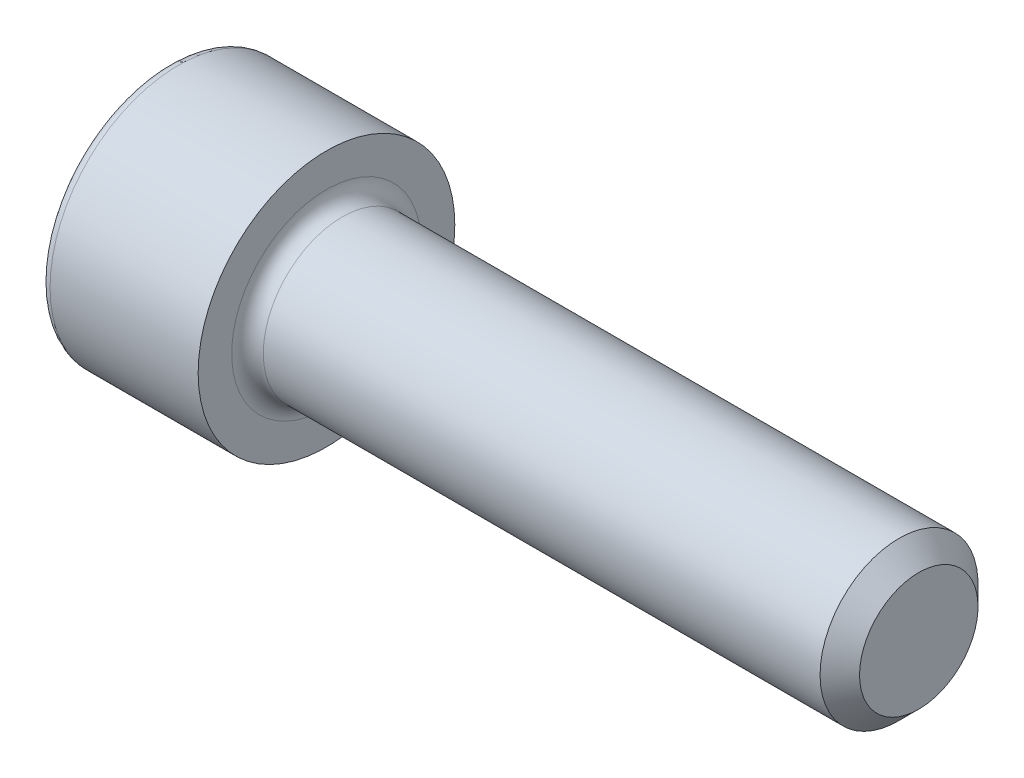
SolidWorks part; units mm, degrees
ref_plane "Plane1" through (0, 0, 0) normal (0, 0, 1) x (1, 0, 0)
ref_plane "Plane2" through (0, 0, 0) normal (0, 1, 0) x (1, 0, 0)
ref_plane "Plane3" through (0, 0, 0) normal (1, 0, 0) x (0, 0, -1)
sketch "BodySke" plane through (0, 0, 0) normal (0, 0, 1) x (1, 0, 0)
  line L0 (0, 0) -> (0, 6.5)
  line L1 (0, 6.5) -> (8, 6.5)
  line L2 (8, 6.5) -> (8, 4)
  line L3 (8, 4) -> (37, 4)
  line L4 (38, 3) -> (38, 0)
  line L5 (38, 0) -> (0, 0)
  line L6 (-31.75, 0) -> (127, 0) construction
  line L8 (38, 3) -> (37, 4)
  line L10 (38, -3) -> (37, -4) construction
  line L11 (5, 9.525) -> (5, 3.175) construction
  line L12 (8, 9.525) -> (8, 3.175) construction
  line L13 (-7, 9.525) -> (-7, 3.175) construction
  dimension "Head_ht" = 8
  dimension "Length" = 30
  dimension "Body_ch_ang" = 45
  dimension "Diameter" = 8
  dimension "Minor_dia" = 6
  dimension "Advance" = 3
  dimension "Thread_nom" = 30
  dimension "Thread_length" = 45
  dimension "Head_dia" = 13
revolve "Base-Revolve" add sketch "BodySke" angle 360 about L6
cosmetic thread "ThreadCosmetic" parameters "Thread_length"=21, "Thread_minor"=6
fillet "Fillet1" radius 0.8 1 edges at (8, 0, 4)
fillet "Fillet2" radius 0.5 1 edges at (0, 0, 6.5)
sketch "Sketch2" plane through (0, 0, 0) normal (0, 0, 1) x (1, 0, 0)
  line L0 (0, 2.8475) -> (12.573, 2.8475)
  line L1 (12.573, 2.8475) -> (14.217, 0)
  line L2 (-31.75, 0) -> (127, 0) construction
  line L3 (14.217, 0) -> (0, 0)
  line L4 (0, 0) -> (0, 2.8475)
  line L6 (0, 0) -> (47.625, 0) construction
  dimension "D1" = 2.8475
  dimension "D2" = 60
  dimension "Depth" = 12.573
revolve "Hex-PreBroach" cut sketch "Sketch2" angle 360 about L6
sketch "Sketch3" plane through (0, 0, 0) normal (-1, 0, 0) x (0, 0.5, 0.866)
  line L0 (1.644, 2.8475) -> (-1.644, 2.8475)
  line L1 (-1.644, 2.8475) -> (-3.288, 0)
  line L2 (1.644, 2.8475) -> (3.288, 0)
  line L3 (1.644, -2.8475) -> (3.288, 0)
  line L4 (1.644, -2.8475) -> (-1.644, -2.8475)
  line L5 (-1.644, -2.8475) -> (-3.288, 0)
  dimension "D1" = 2.8475
  dimension "D2" = 2.8475
  dimension "Hex_size" = 5.695
extrude "Hex" cut sketch "Sketch3" against normal blind 12.573
sketch "ThdSchSke" plane through (0, 0, 0) normal (0, 0, 1) x (1, 0, 0)
  line L0 (17, -3) -> (16.2998, -4)
  line L1 (17, -3) -> (17.7002, -4)
  line L2 (17.7002, -4) -> (17.7002, -5)
  line L3 (-3.175, 0) -> (5.1513, 0) construction
  line L4 (0, 6) -> (0, -6) construction
  line L5 (17.7002, -5) -> (16.2998, -5)
  line L6 (16.2998, -5) -> (16.2998, -4)
  dimension "Thread_minor" = 6
  dimension "Diameter" = 8
  dimension "SideAngle" = 55
  dimension "VeeAngle" = 70
  dimension "Overcut" = 10
  dimension "Start" = 17
revolve "ThreadSchematic" [suppressed] cut sketch "ThdSchSke" angle 360 about L3
pattern_linear "ThdSchPat" [suppressed]
equation "\"D2@Sketch3\" = \"Hex_size@Sketch3\" / 2"
equation "\"D1@Sketch3\" = \"Hex_size@Sketch3\" / 2"
equation "\"D1@Sketch2\" = \"Hex_size@Sketch3\" / 2"
equation "\"Thread_minor@ThreadCosmetic\"  =  \"Minor_dia@BodySke\""
equation "\"Depth@Sketch2\" =  \"Key_eng@Hex\""
equation "\"Thread_length@ThreadCosmetic\" = ((sgn( (\"Length@BodySke\" - \"Advance@BodySke\" * 3.0) - \"Thread_nom@BodySke\" )-1)*( (\"Length@BodySke\" - \"Advance@BodySke\" * 3.0) - \"Thread_nom@BodySke\" ))/-2+ \"Thread_nom@BodySke\""
equation "\"Thread_minor@ThdSchSke\" = \"Minor_dia@BodySke\""
equation "\"Diameter@ThdSchSke\" = \"Diameter@BodySke\""
equation "\"Overcut@ThdSchSke\" = \"Diameter@BodySke\" * 1.25"
equation "\"Start@ThdSchSke\" = \"Head_ht@BodySke\" + \"Length@BodySke\" - \"Thread_length@ThreadCosmetic\"  '---Non-countersunk---"
equation "\"Num_threads@ThdSchPat\" = int( \"Thread_length@ThreadCosmetic\" / \"Advance@BodySke\" + 0.999 )  + 1"
equation "\"Advance@ThdSchPat\" = \"Thread_length@ThreadCosmetic\" /  (\"Num_threads@ThdSchPat\" - 1) 'relax it"
equation "\"Num_threads@ThdSchPat\" = \"Num_threads@ThdSchPat\" - sgn( \"Num_threads@ThdSchPat\" - 1) '---chamfered tips only---"
